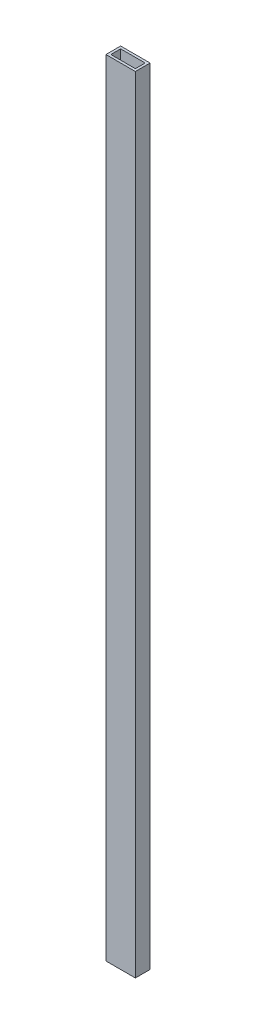
SolidWorks part; units mm, degrees
ref_plane "Front" through (0, 0, 0) normal (0, 0, 1) x (1, 0, 0)
ref_plane "Top" through (0, 0, 0) normal (0, 1, 0) x (1, 0, 0)
ref_plane "Right" through (0, 0, 0) normal (1, 0, 0) x (0, 0, -1)
sketch "Sketch1" plane through (0, 0, 0) normal (0, 1, 0) x (1, 0, 0)
  line L0 (3.175, 3.175) -> (34.925, 3.175)
  line L1 (0, 0) -> (38.1, 0)
  line L2 (0, 0) -> (0, 19.05)
  line L3 (0, 19.05) -> (38.1, 19.05)
  line L4 (38.1, 0) -> (38.1, 19.05)
  line L5 (34.925, 3.175) -> (34.925, 15.875)
  line L6 (3.175, 15.875) -> (34.925, 15.875)
  line L7 (3.175, 3.175) -> (3.175, 15.875)
  dimension "D1" = 38.1
  dimension "D2" = 19.05
  dimension "D3" = 3.175
extrude "Boss-Extrude1" add sketch "Sketch1" along normal blind 1016
